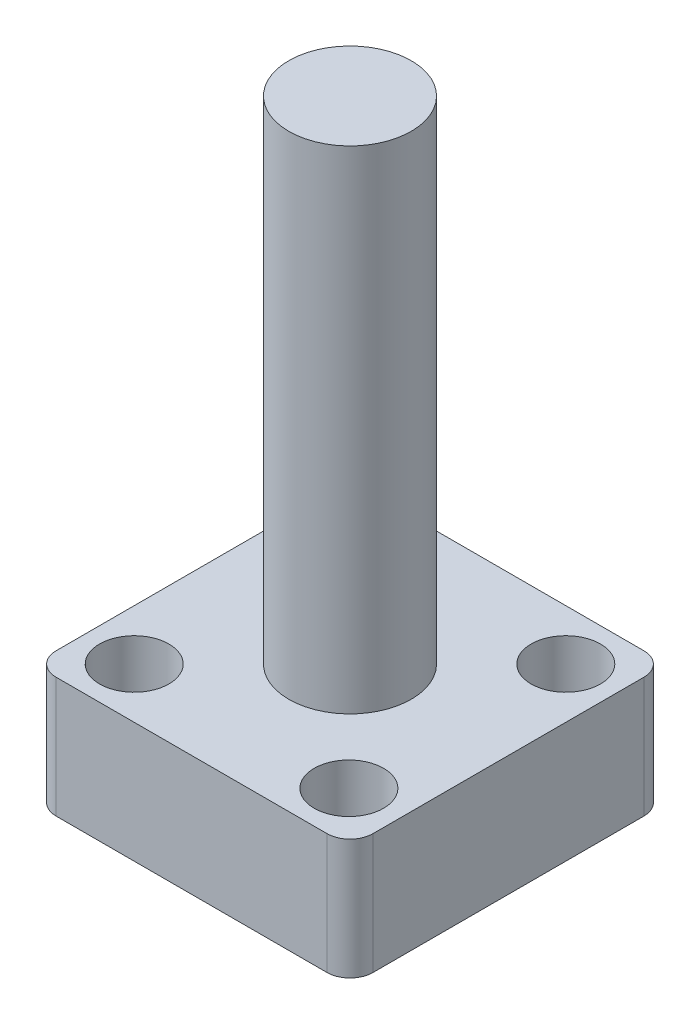
SolidWorks part; units mm, degrees
ref_plane "Front Plane" through (0, 0, 0) normal (0, 0, 1) x (1, 0, 0)
ref_plane "Top Plane" through (0, 0, 0) normal (0, 1, 0) x (1, 0, 0)
ref_plane "Right Plane" through (0, 0, 0) normal (1, 0, 0) x (0, 0, -1)
sketch "Sketch1" plane through (0, 0, 0) normal (0, 1, 0) x (1, 0, 0)
  line L1 (26.289, -26.289) -> (-26.289, -26.289)
  line L2 (26.289, -26.289) -> (26.289, 26.289)
  line L3 (26.289, 26.289) -> (-26.289, 26.289)
  line L4 (-26.289, -26.289) -> (-26.289, 26.289)
  line L5 (26.289, -26.289) -> (-26.289, 26.289) construction
  line L6 (26.289, 26.289) -> (-26.289, -26.289) construction
  point P0 (0, 0)
  dimension "D1" = 52.578
  dimension "D2" = 52.578
extrude "Extrude1" add sketch "Sketch1" along normal blind 19.9644
sketch "Sketch2" plane through (0, 19.9644, 0) normal (0, 1, 0) x (1, 0, 0)
  line L0 (-26.289, 26.289) -> (26.289, -26.289) construction
  line L1 (-26.289, -26.289) -> (26.289, 26.289) construction
  line L2 (-17.907, 17.907) -> (17.907, 17.907) construction
  line L3 (-17.907, 17.907) -> (-17.907, -17.907) construction
  line L4 (-17.907, -17.907) -> (17.907, -17.907) construction
  line L5 (17.907, 17.907) -> (17.907, -26.289) construction
  line L6 (-26.289, -26.289) -> (26.289, -26.289) construction
  circle A0 centre (-17.907, 17.907) radius 2.667
  circle A1 centre (-17.907, -17.907) radius 2.667
  circle A2 centre (18.0213, -17.6956) radius 2.667
  circle A3 centre (17.907, 17.907) radius 2.667
  point P15 (0, 0)
  point P22 (0, 0)
  dimension "D1" = 5.334
  dimension "D3" = 5.334
  dimension "D4" = 5.334
  dimension "D5" = 5.334
  dimension "D2" = 35.814
extrude "Extrude2" cut sketch "Sketch2" along normal blind 5.7658 from surface at -19.9644 starting at face at (0, 0, 0)
sketch "Sketch6" plane through (0, 0, 0) normal (0, -1, 0) x (1, 0, 0)
  circle A0 centre (-17.907, -17.907) radius 5.7544
  circle A1 centre (-17.907, 17.907) radius 5.7544
  circle A2 centre (17.7728, 17.9563) radius 5.7544
  circle A3 centre (17.907, -17.907) radius 5.7544
  dimension "D1" = 11.5087
  dimension "D2" = 11.5087
  dimension "D4" = 11.5087
extrude "Extrude4" cut sketch "Sketch6" along normal up to surface (14.1986 mm away) from surface at -19.9644 up to face at (17.907, 5.7658, -15.24) starting at face at (0, 19.9644, 0)
fillet "Fillet2" radius 3.81 4 edges at (-26.289, 9.9822, -26.289) (26.289, 9.9822, -26.289) (-26.289, 9.9822, 26.289) (26.289, 9.9822, 26.289)
sketch "Sketch7" plane through (0, 0, 0) normal (0, 1, 0) x (1, 0, 0)
  circle A0 centre (0, 0) radius 10.16
  dimension "D1" = 20.32
extrude "Boss-Extrude1" add sketch "Sketch7" along normal blind 101.6
